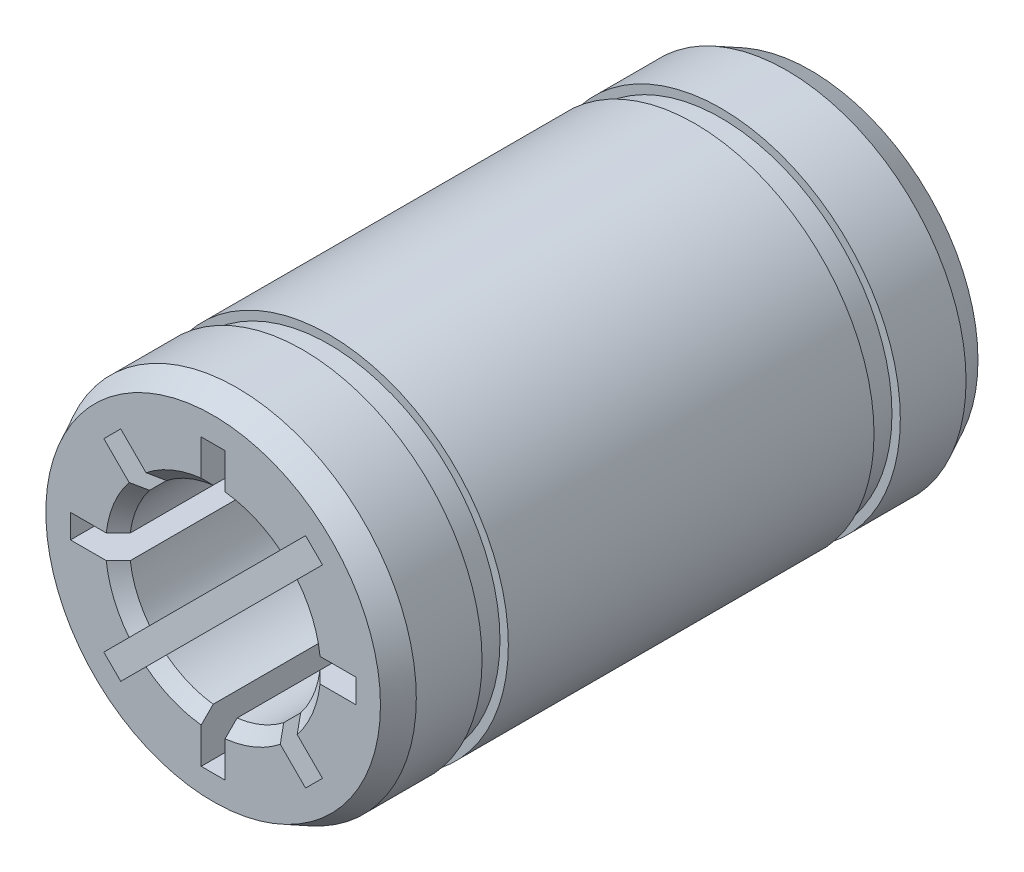
SolidWorks part; units mm, degrees
material "Delrin 2700 NC010, copolymère d'acétal à faible viscosité (SS)"
ref_plane "Plan de face" through (0, 0, 0) normal (0, 0, 1) x (1, 0, 0)
ref_plane "Plan de dessus" through (0, 0, 0) normal (0, 1, 0) x (1, 0, 0)
ref_plane "Plan de droite" through (0, 0, 0) normal (1, 0, 0) x (0, 0, -1)
sketch "Esquisse1" plane through (0, 0, 0) normal (0, 0, 1) x (1, 0, 0)
  line L0 (3.8669, 4.574) -> (2.4527, 3.1598)
  line L1 (-0.5, 5.9686) -> (0.5, 5.9686)
  line L2 (-0.5, 5.9686) -> (-0.5, 3.9686)
  line L3 (3.8669, 4.574) -> (4.574, 3.8669)
  line L4 (0.5, 5.9686) -> (0.5, 3.9686)
  line L5 (4.574, 3.8669) -> (3.1598, 2.4527)
  line L6 (5.9686, 0.5) -> (3.9686, 0.5)
  line L7 (5.9686, 0.5) -> (5.9686, -0.5)
  line L8 (5.9686, -0.5) -> (3.9686, -0.5)
  line L9 (4.574, -3.8669) -> (3.1598, -2.4527)
  line L10 (4.574, -3.8669) -> (3.8669, -4.574)
  line L11 (3.8669, -4.574) -> (2.4527, -3.1598)
  line L12 (0.5, -5.9686) -> (0.5, -3.9686)
  line L13 (0.5, -5.9686) -> (-0.5, -5.9686)
  line L14 (-0.5, -5.9686) -> (-0.5, -3.9686)
  line L15 (-3.8669, -4.574) -> (-2.4527, -3.1598)
  line L16 (-3.8669, -4.574) -> (-4.574, -3.8669)
  line L17 (-4.574, -3.8669) -> (-3.1598, -2.4527)
  line L18 (-5.9686, -0.5) -> (-3.9686, -0.5)
  line L19 (-5.9686, -0.5) -> (-5.9686, 0.5)
  line L20 (-5.9686, 0.5) -> (-3.9686, 0.5)
  line L21 (-4.574, 3.8669) -> (-3.1598, 2.4527)
  line L22 (-4.574, 3.8669) -> (-3.8669, 4.574)
  line L23 (-3.8669, 4.574) -> (-2.4527, 3.1598)
  circle A0 centre (0, 0) radius 7.5
  arc A1 (-3.1598, 2.4527) -> (-3.9686, 0.5) centre (0, 0) ccw
  arc A2 (2.4527, 3.1598) -> (0.5, 3.9686) centre (0, 0) ccw
  arc A3 (-0.5, 3.9686) -> (-2.4527, 3.1598) centre (0, 0) ccw
  arc A4 (3.9686, 0.5) -> (3.1598, 2.4527) centre (0, 0) ccw
  arc A5 (3.1598, -2.4527) -> (3.9686, -0.5) centre (0, 0) ccw
  arc A6 (0.5, -3.9686) -> (2.4527, -3.1598) centre (0, 0) ccw
  arc A7 (-2.4527, -3.1598) -> (-0.5, -3.9686) centre (0, 0) ccw
  arc A8 (-3.9686, -0.5) -> (-3.1598, -2.4527) centre (0, 0) ccw
  point P38 (0, 0)
  dimension "D1" = 15
  dimension "D2" = 8
  dimension "D3" = 1
  dimension "D4" = 0.5
  dimension "D5" = 2
  dimension "D6" = 8
extrude "Boss.-Extru.1" add sketch "Esquisse1" along normal mid plane 25
ref_axis "Axe1" through (0, 0, 12.5) along (0, 0, -1)
sketch "Esquisse2" plane through (0, 0, 0) normal (1, 0, 0) x (0, 0, -1)
  line L0 (12.5, 7.5) -> (-12.5, 7.5) construction
  line L1 (-8.75, 7.5) -> (-7.65, 7.5)
  line L2 (-8.75, 7.5) -> (-8.75, 7.15)
  line L3 (-8.75, 7.15) -> (-7.65, 7.15)
  line L4 (-7.65, 7.5) -> (-7.65, 7.15)
  line L5 (7.65, 7.5) -> (8.75, 7.5)
  line L6 (7.65, 7.5) -> (7.65, 7.15)
  line L7 (7.65, 7.15) -> (8.75, 7.15)
  line L8 (8.75, 7.5) -> (8.75, 7.15)
  dimension "D1" = 17.5
  dimension "D2" = 8.75
  dimension "D3" = 1.1
  dimension "D4" = 0.35
revolve "Enlèvement de matière-Révolution1" cut sketch "Esquisse2" angle 360 about axis through (0, 0, 12.5) along (0, 0, -1)
chamfer "Chanfrein1" distance 1 distance2 0.5 1 edges at (7.5, 0, 12.5)
chamfer "Chanfrein2" distance 0.5 distance2 1 1 edges at (7.5, 0, -12.5)
chamfer "Chanfrein3" distance 0.5 angle 45 16 edges at (-3.6955, -1.5307, 12.5) (-1.5307, -3.6955, 12.5) (1.5307, -3.6955, 12.5) (3.6955, -1.5307, 12.5) (3.6955, 1.5307, 12.5) (1.5307, 3.6955, 12.5) (-1.5307, 3.6955, 12.5) (-3.6955, 1.5307, 12.5) (3.6955, 1.5307, -12.5) (3.6955, -1.5307, -12.5) (1.5307, -3.6955, -12.5) (-1.5307, -3.6955, -12.5) (-3.6955, -1.5307, -12.5) (-3.6955, 1.5307, -12.5) (-1.5307, 3.6955, -12.5) (1.5307, 3.6955, -12.5)
equation "\"D4@Esquisse1\"=\"D3@Esquisse1\"/2"
equation "\"D2@Esquisse2\"=\"D1@Esquisse2\"/2"
